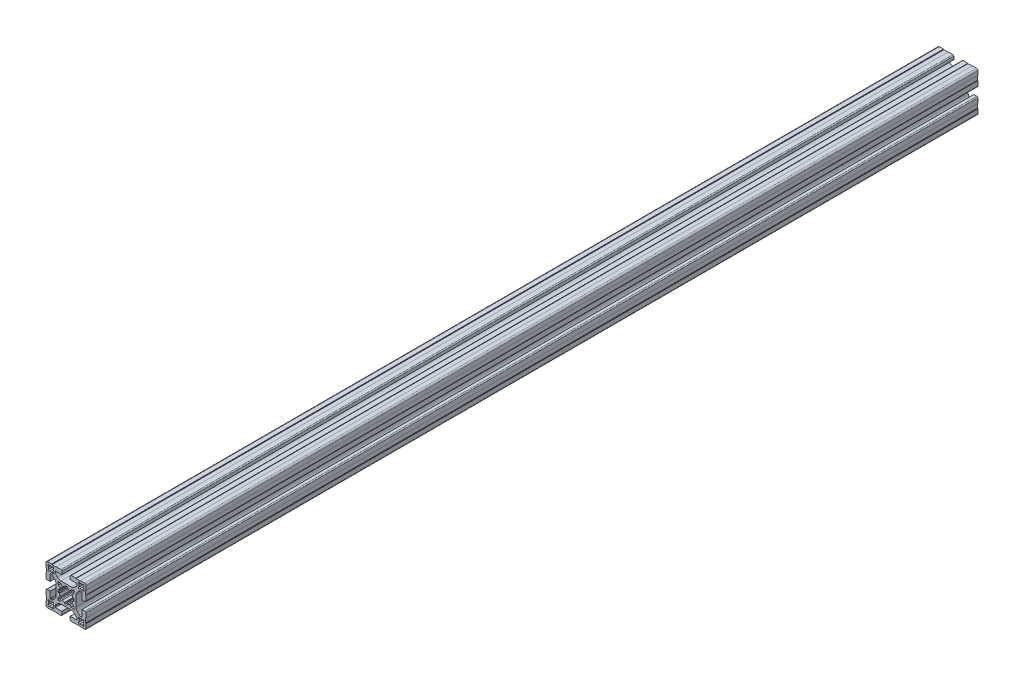
SolidWorks part; units mm, degrees
ref_plane "Plano frontal" through (0, 0, 0) normal (0, 0, 1) x (1, 0, 0)
ref_plane "Plano superior" through (0, 0, 0) normal (0, 1, 0) x (1, 0, 0)
ref_plane "Plano direito" through (0, 0, 0) normal (1, 0, 0) x (0, 0, -1)
sketch "Esboço1" plane through (0, 0, 0) normal (0, 0, 1) x (1, 0, 0)
  point P0 (0, 0)
  line B0 (-17.8572, 16.7966) -> (-17.4167, 16.356)
  arc B1 (-16.7966, 17.8572) -> (-17.8572, 16.7966) centre (-17.3269, 17.3269) ccw
  line B2 (-16.356, 17.4167) -> (-16.7966, 17.8572)
  arc B3 (-14.044, 17.4167) -> (-16.356, 17.4167) centre (-15.2, 15.2) ccw
  line B4 (-13.6034, 17.8572) -> (-14.044, 17.4167)
  arc B5 (-12.5428, 16.7966) -> (-13.6034, 17.8572) centre (-13.0731, 17.3269) ccw
  line B6 (-12.9833, 16.356) -> (-12.5428, 16.7966)
  arc B7 (-12.9833, 14.044) -> (-12.9833, 16.356) centre (-15.2, 15.2) ccw
  line B8 (-12.5428, 13.6034) -> (-12.9833, 14.044)
  arc B9 (-13.6034, 12.5428) -> (-12.5428, 13.6034) centre (-13.0731, 13.0731) ccw
  line B10 (-14.044, 12.9833) -> (-13.6034, 12.5428)
  arc B11 (-16.356, 12.9833) -> (-14.044, 12.9833) centre (-15.2, 15.2) ccw
  line B12 (-16.7966, 12.5428) -> (-16.356, 12.9833)
  arc B13 (-17.8572, 13.6034) -> (-16.7966, 12.5428) centre (-17.3269, 13.0731) ccw
  line B14 (-17.4167, 14.044) -> (-17.8572, 13.6034)
  arc B15 (-17.4167, 16.356) -> (-17.4167, 14.044) centre (-15.2, 15.2) ccw
  line B16 (17.4167, 14.044) -> (17.8572, 13.6034)
  arc B17 (16.7966, 12.5428) -> (17.8572, 13.6034) centre (17.3269, 13.0731) ccw
  line B18 (16.7966, 12.5428) -> (16.356, 12.9833)
  arc B19 (14.044, 12.9833) -> (16.356, 12.9833) centre (15.2, 15.2) ccw
  line B20 (14.044, 12.9833) -> (13.6034, 12.5428)
  arc B21 (12.5428, 13.6034) -> (13.6034, 12.5428) centre (13.0731, 13.0731) ccw
  line B22 (12.5428, 13.6034) -> (12.9833, 14.044)
  arc B23 (12.9833, 16.356) -> (12.9833, 14.044) centre (15.2, 15.2) ccw
  line B24 (12.9833, 16.356) -> (12.5428, 16.7966)
  arc B25 (13.6034, 17.8572) -> (12.5428, 16.7966) centre (13.0731, 17.3269) ccw
  line B26 (13.6034, 17.8572) -> (14.044, 17.4167)
  arc B27 (16.356, 17.4167) -> (14.044, 17.4167) centre (15.2, 15.2) ccw
  line B28 (16.356, 17.4167) -> (16.7966, 17.8572)
  arc B29 (17.8572, 16.7966) -> (16.7966, 17.8572) centre (17.3269, 17.3269) ccw
  line B30 (17.8572, 16.7966) -> (17.4167, 16.356)
  arc B31 (17.4167, 14.044) -> (17.4167, 16.356) centre (15.2, 15.2) ccw
  line B32 (-17.4167, -14.044) -> (-17.8572, -13.6034)
  arc B33 (-16.7966, -12.5428) -> (-17.8572, -13.6034) centre (-17.3269, -13.0731) ccw
  line B34 (-16.7966, -12.5428) -> (-16.356, -12.9833)
  arc B35 (-14.044, -12.9833) -> (-16.356, -12.9833) centre (-15.2, -15.2) ccw
  line B36 (-14.044, -12.9833) -> (-13.6034, -12.5428)
  arc B37 (-12.5428, -13.6034) -> (-13.6034, -12.5428) centre (-13.0731, -13.0731) ccw
  line B38 (-12.5428, -13.6034) -> (-12.9833, -14.044)
  arc B39 (-12.9833, -16.356) -> (-12.9833, -14.044) centre (-15.2, -15.2) ccw
  line B40 (-12.9833, -16.356) -> (-12.5428, -16.7966)
  arc B41 (-13.6034, -17.8572) -> (-12.5428, -16.7966) centre (-13.0731, -17.3269) ccw
  line B42 (-13.6034, -17.8572) -> (-14.044, -17.4167)
  arc B43 (-16.356, -17.4167) -> (-14.044, -17.4167) centre (-15.2, -15.2) ccw
  line B44 (-16.356, -17.4167) -> (-16.7966, -17.8572)
  arc B45 (-17.8572, -16.7966) -> (-16.7966, -17.8572) centre (-17.3269, -17.3269) ccw
  line B46 (-17.8572, -16.7966) -> (-17.4167, -16.356)
  arc B47 (-17.4167, -14.044) -> (-17.4167, -16.356) centre (-15.2, -15.2) ccw
  line B48 (17.8572, -16.7966) -> (17.4167, -16.356)
  arc B49 (16.7966, -17.8572) -> (17.8572, -16.7966) centre (17.3269, -17.3269) ccw
  line B50 (16.356, -17.4167) -> (16.7966, -17.8572)
  arc B51 (14.044, -17.4167) -> (16.356, -17.4167) centre (15.2, -15.2) ccw
  line B52 (13.6034, -17.8572) -> (14.044, -17.4167)
  arc B53 (12.5428, -16.7966) -> (13.6034, -17.8572) centre (13.0731, -17.3269) ccw
  line B54 (12.9833, -16.356) -> (12.5428, -16.7966)
  arc B55 (12.9833, -14.044) -> (12.9833, -16.356) centre (15.2, -15.2) ccw
  line B56 (12.5428, -13.6034) -> (12.9833, -14.044)
  arc B57 (13.6034, -12.5428) -> (12.5428, -13.6034) centre (13.0731, -13.0731) ccw
  line B58 (14.044, -12.9833) -> (13.6034, -12.5428)
  arc B59 (16.356, -12.9833) -> (14.044, -12.9833) centre (15.2, -15.2) ccw
  line B60 (16.7966, -12.5428) -> (16.356, -12.9833)
  arc B61 (17.8572, -13.6034) -> (16.7966, -12.5428) centre (17.3269, -13.0731) ccw
  line B62 (17.4167, -14.044) -> (17.8572, -13.6034)
  arc B63 (17.4167, -16.356) -> (17.4167, -14.044) centre (15.2, -15.2) ccw
  line B64 (4.15, -18.8) -> (4.15, -15.9)
  arc B65 (4.25, -15.8) -> (4.15, -15.9) centre (4.25, -15.9) ccw
  line B66 (4.25, -15.8) -> (10.5, -15.8)
  arc B67 (10.5, -15.8) -> (11, -15.3) centre (10.5, -15.3) ccw
  line B68 (11, -15.3) -> (11, -14.4497)
  arc B69 (11, -14.4497) -> (10.5607, -13.3891) centre (9.5, -14.4497) ccw
  line B70 (10.5607, -13.3891) -> (8.636, -11.4645)
  arc B71 (8.636, -11.4645) -> (5.1005, -10) centre (5.1005, -15) ccw
  line B72 (5.1005, -10) -> (0, -10)
  line B73 (0, -10) -> (-5.1005, -10)
  arc B74 (-5.1005, -10) -> (-8.636, -11.4645) centre (-5.1005, -15) ccw
  line B75 (-8.636, -11.4645) -> (-10.5607, -13.3891)
  arc B76 (-10.5607, -13.3891) -> (-11, -14.4497) centre (-9.5, -14.4497) ccw
  line B77 (-11, -14.4497) -> (-11, -15.3)
  arc B78 (-11, -15.3) -> (-10.5, -15.8) centre (-10.5, -15.3) ccw
  line B79 (-10.5, -15.8) -> (-4.25, -15.8)
  arc B80 (-4.15, -15.9) -> (-4.25, -15.8) centre (-4.25, -15.9) ccw
  line B81 (-4.15, -15.9) -> (-4.15, -18.8)
  arc B82 (-5.15, -19.8) -> (-4.15, -18.8) centre (-5.15, -18.8) ccw
  line B83 (-5.15, -19.8) -> (-9.8, -19.8)
  line B84 (-9.8, -19.8) -> (-10, -19.6)
  line B85 (-10, -19.6) -> (-14, -19.6)
  line B86 (-14, -19.6) -> (-14.4, -20)
  line B87 (-14.4, -20) -> (-18.5, -20)
  arc B88 (-20, -18.5) -> (-18.5, -20) centre (-18.5, -18.5) ccw
  line B89 (-20, -18.5) -> (-20, -14.4)
  line B90 (-20, -14.4) -> (-19.6, -14)
  line B91 (-19.6, -14) -> (-19.6, -10)
  line B92 (-19.6, -10) -> (-19.8, -9.8)
  line B93 (-19.8, -9.8) -> (-19.8, -5.15)
  arc B94 (-18.8, -4.15) -> (-19.8, -5.15) centre (-18.8, -5.15) ccw
  line B95 (-18.8, -4.15) -> (-15.9, -4.15)
  arc B96 (-15.8, -4.25) -> (-15.9, -4.15) centre (-15.9, -4.25) ccw
  line B97 (-15.8, -4.25) -> (-15.8, -10.5)
  arc B98 (-15.8, -10.5) -> (-15.3, -11) centre (-15.3, -10.5) ccw
  line B99 (-15.3, -11) -> (-14.4497, -11)
  arc B100 (-14.4497, -11) -> (-13.3891, -10.5607) centre (-14.4497, -9.5) ccw
  line B101 (-13.3891, -10.5607) -> (-11.4645, -8.636)
  arc B102 (-11.4645, -8.636) -> (-10, -5.1005) centre (-15, -5.1005) ccw
  line B103 (-10, -5.1005) -> (-10, 0)
  line B104 (-10, 0) -> (-10, 5.1005)
  arc B105 (-10, 5.1005) -> (-11.4645, 8.636) centre (-15, 5.1005) ccw
  line B106 (-11.4645, 8.636) -> (-13.3891, 10.5607)
  arc B107 (-13.3891, 10.5607) -> (-14.4497, 11) centre (-14.4497, 9.5) ccw
  line B108 (-14.4497, 11) -> (-15.3, 11)
  arc B109 (-15.3, 11) -> (-15.8, 10.5) centre (-15.3, 10.5) ccw
  line B110 (-15.8, 10.5) -> (-15.8, 4.25)
  arc B111 (-15.9, 4.15) -> (-15.8, 4.25) centre (-15.9, 4.25) ccw
  line B112 (-15.9, 4.15) -> (-18.8, 4.15)
  arc B113 (-19.8, 5.15) -> (-18.8, 4.15) centre (-18.8, 5.15) ccw
  line B114 (-19.8, 5.15) -> (-19.8, 9.8)
  line B115 (-19.8, 9.8) -> (-19.6, 10)
  line B116 (-19.6, 10) -> (-19.6, 14)
  line B117 (-19.6, 14) -> (-20, 14.4)
  line B118 (-20, 14.4) -> (-20, 18.5)
  arc B119 (-18.5, 20) -> (-20, 18.5) centre (-18.5, 18.5) ccw
  line B120 (-18.5, 20) -> (-14.4, 20)
  line B121 (-14.4, 20) -> (-14, 19.6)
  line B122 (-14, 19.6) -> (-10, 19.6)
  line B123 (-10, 19.6) -> (-9.8, 19.8)
  line B124 (-9.8, 19.8) -> (-5.15, 19.8)
  arc B125 (-4.15, 18.8) -> (-5.15, 19.8) centre (-5.15, 18.8) ccw
  line B126 (-4.15, 18.8) -> (-4.15, 15.9)
  arc B127 (-4.25, 15.8) -> (-4.15, 15.9) centre (-4.25, 15.9) ccw
  line B128 (-4.25, 15.8) -> (-10.5, 15.8)
  arc B129 (-10.5, 15.8) -> (-11, 15.3) centre (-10.5, 15.3) ccw
  line B130 (-11, 15.3) -> (-11, 14.4497)
  arc B131 (-11, 14.4497) -> (-10.5607, 13.3891) centre (-9.5, 14.4497) ccw
  line B132 (-10.5607, 13.3891) -> (-8.636, 11.4645)
  arc B133 (-8.636, 11.4645) -> (-5.1005, 10) centre (-5.1005, 15) ccw
  line B134 (-5.1005, 10) -> (0, 10)
  line B135 (0, 10) -> (5.1005, 10)
  arc B136 (5.1005, 10) -> (8.636, 11.4645) centre (5.1005, 15) ccw
  line B137 (8.636, 11.4645) -> (10.5607, 13.3891)
  arc B138 (10.5607, 13.3891) -> (11, 14.4497) centre (9.5, 14.4497) ccw
  line B139 (11, 14.4497) -> (11, 15.3)
  arc B140 (11, 15.3) -> (10.5, 15.8) centre (10.5, 15.3) ccw
  line B141 (10.5, 15.8) -> (4.25, 15.8)
  arc B142 (4.15, 15.9) -> (4.25, 15.8) centre (4.25, 15.9) ccw
  line B143 (4.15, 15.9) -> (4.15, 18.8)
  arc B144 (5.15, 19.8) -> (4.15, 18.8) centre (5.15, 18.8) ccw
  line B145 (5.15, 19.8) -> (9.8, 19.8)
  line B146 (9.8, 19.8) -> (10, 19.6)
  line B147 (10, 19.6) -> (14, 19.6)
  line B148 (14, 19.6) -> (14.4, 20)
  line B149 (14.4, 20) -> (18.5, 20)
  arc B150 (20, 18.5) -> (18.5, 20) centre (18.5, 18.5) ccw
  line B151 (20, 18.5) -> (20, 14.4)
  line B152 (20, 14.4) -> (19.6, 14)
  line B153 (19.6, 14) -> (19.6, 10)
  line B154 (19.6, 10) -> (19.8, 9.8)
  line B155 (19.8, 9.8) -> (19.8, 5.15)
  arc B156 (18.8, 4.15) -> (19.8, 5.15) centre (18.8, 5.15) ccw
  line B157 (18.8, 4.15) -> (15.9, 4.15)
  arc B158 (15.8, 4.25) -> (15.9, 4.15) centre (15.9, 4.25) ccw
  line B159 (15.8, 4.25) -> (15.8, 10.5)
  arc B160 (15.8, 10.5) -> (15.3, 11) centre (15.3, 10.5) ccw
  line B161 (15.3, 11) -> (14.4497, 11)
  arc B162 (14.4497, 11) -> (13.3891, 10.5607) centre (14.4497, 9.5) ccw
  line B163 (13.3891, 10.5607) -> (11.4645, 8.636)
  arc B164 (11.4645, 8.636) -> (10, 5.1005) centre (15, 5.1005) ccw
  line B165 (10, 5.1005) -> (10, 0)
  line B166 (10, 0) -> (10, -5.1005)
  arc B167 (10, -5.1005) -> (11.4645, -8.636) centre (15, -5.1005) ccw
  line B168 (11.4645, -8.636) -> (13.3891, -10.5607)
  arc B169 (13.3891, -10.5607) -> (14.4497, -11) centre (14.4497, -9.5) ccw
  line B170 (14.4497, -11) -> (15.3, -11)
  arc B171 (15.3, -11) -> (15.8, -10.5) centre (15.3, -10.5) ccw
  line B172 (15.8, -10.5) -> (15.8, -4.25)
  arc B173 (15.9, -4.15) -> (15.8, -4.25) centre (15.9, -4.25) ccw
  line B174 (15.9, -4.15) -> (18.8, -4.15)
  arc B175 (19.8, -5.15) -> (18.8, -4.15) centre (18.8, -5.15) ccw
  line B176 (19.8, -5.15) -> (19.8, -9.8)
  line B177 (19.8, -9.8) -> (19.6, -10)
  line B178 (19.6, -10) -> (19.6, -14)
  line B179 (19.6, -14) -> (20, -14.4)
  line B180 (20, -14.4) -> (20, -18.5)
  arc B181 (18.5, -20) -> (20, -18.5) centre (18.5, -18.5) ccw
  line B182 (18.5, -20) -> (14.4, -20)
  line B183 (14.4, -20) -> (14, -19.6)
  line B184 (14, -19.6) -> (10, -19.6)
  line B185 (10, -19.6) -> (9.8, -19.8)
  line B186 (9.8, -19.8) -> (5.15, -19.8)
  arc B187 (4.15, -18.8) -> (5.15, -19.8) centre (5.15, -18.8) ccw
  line B188 (-5.3139, -7.6355) -> (-7.6488, -8.2611)
  arc B189 (-8.2611, -7.6488) -> (-7.6488, -8.2611) centre (-7.7782, -7.7782) ccw
  line B190 (-8.2611, -7.6488) -> (-7.6355, -5.3139)
  arc B191 (-7.4569, -5.0466) -> (-7.6355, -5.3139) centre (-7.1525, -5.4433) ccw
  line B192 (-7.4569, -5.0466) -> (-5.744, -3.7322)
  arc B193 (-6.7007, -1.4225) -> (-5.744, -3.7322) centre (0, 0) ccw
  line B194 (-6.7007, -1.4225) -> (-7.5204, -1.3146)
  arc B195 (-7.9522, -0.8735) -> (-7.5204, -1.3146) centre (-7.4552, -0.8189) ccw
  arc B196 (-7.9522, 0.8735) -> (-7.9522, -0.8735) centre (0, 0) ccw
  arc B197 (-7.5204, 1.3146) -> (-7.9522, 0.8735) centre (-7.4552, 0.8189) ccw
  line B198 (-7.5204, 1.3146) -> (-6.7007, 1.4225)
  arc B199 (-5.744, 3.7322) -> (-6.7007, 1.4225) centre (0, 0) ccw
  line B200 (-5.744, 3.7322) -> (-7.4569, 5.0466)
  arc B201 (-7.6355, 5.3139) -> (-7.4569, 5.0466) centre (-7.1525, 5.4433) ccw
  line B202 (-7.6355, 5.3139) -> (-8.2611, 7.6488)
  arc B203 (-7.6488, 8.2611) -> (-8.2611, 7.6488) centre (-7.7782, 7.7782) ccw
  line B204 (-7.6488, 8.2611) -> (-5.3139, 7.6355)
  arc B205 (-5.0466, 7.4569) -> (-5.3139, 7.6355) centre (-5.4433, 7.1525) ccw
  line B206 (-5.0466, 7.4569) -> (-3.7322, 5.744)
  arc B207 (-1.4225, 6.7007) -> (-3.7322, 5.744) centre (0, 0) ccw
  line B208 (-1.4225, 6.7007) -> (-1.3146, 7.5204)
  arc B209 (-0.8735, 7.9522) -> (-1.3146, 7.5204) centre (-0.8189, 7.4552) ccw
  arc B210 (0.8735, 7.9522) -> (-0.8735, 7.9522) centre (0, 0) ccw
  arc B211 (1.3146, 7.5204) -> (0.8735, 7.9522) centre (0.8189, 7.4552) ccw
  line B212 (1.3146, 7.5204) -> (1.4225, 6.7007)
  arc B213 (3.7322, 5.744) -> (1.4225, 6.7007) centre (0, 0) ccw
  line B214 (3.7322, 5.744) -> (5.0466, 7.4569)
  arc B215 (5.3139, 7.6355) -> (5.0466, 7.4569) centre (5.4433, 7.1525) ccw
  line B216 (5.3139, 7.6355) -> (7.6488, 8.2611)
  arc B217 (8.2611, 7.6488) -> (7.6488, 8.2611) centre (7.7782, 7.7782) ccw
  line B218 (8.2611, 7.6488) -> (7.6355, 5.3139)
  arc B219 (7.4569, 5.0466) -> (7.6355, 5.3139) centre (7.1525, 5.4433) ccw
  line B220 (7.4569, 5.0466) -> (5.744, 3.7322)
  arc B221 (6.7007, 1.4225) -> (5.744, 3.7322) centre (0, 0) ccw
  line B222 (6.7007, 1.4225) -> (7.5204, 1.3146)
  arc B223 (7.9522, 0.8735) -> (7.5204, 1.3146) centre (7.4552, 0.8189) ccw
  arc B224 (7.9522, -0.8735) -> (7.9522, 0.8735) centre (0, 0) ccw
  arc B225 (7.5204, -1.3146) -> (7.9522, -0.8735) centre (7.4552, -0.8189) ccw
  line B226 (7.5204, -1.3146) -> (6.7007, -1.4225)
  arc B227 (5.744, -3.7322) -> (6.7007, -1.4225) centre (0, 0) ccw
  line B228 (5.744, -3.7322) -> (7.4569, -5.0466)
  arc B229 (7.6355, -5.3139) -> (7.4569, -5.0466) centre (7.1525, -5.4433) ccw
  line B230 (7.6355, -5.3139) -> (8.2611, -7.6488)
  arc B231 (7.6488, -8.2611) -> (8.2611, -7.6488) centre (7.7782, -7.7782) ccw
  line B232 (7.6488, -8.2611) -> (5.3139, -7.6355)
  arc B233 (5.0466, -7.4569) -> (5.3139, -7.6355) centre (5.4433, -7.1525) ccw
  line B234 (5.0466, -7.4569) -> (3.7322, -5.744)
  arc B235 (1.4225, -6.7007) -> (3.7322, -5.744) centre (0, 0) ccw
  line B236 (1.4225, -6.7007) -> (1.3146, -7.5204)
  arc B237 (0.8735, -7.9522) -> (1.3146, -7.5204) centre (0.8189, -7.4552) ccw
  arc B238 (-0.8735, -7.9522) -> (0.8735, -7.9522) centre (0, 0) ccw
  arc B239 (-1.3146, -7.5204) -> (-0.8735, -7.9522) centre (-0.8189, -7.4552) ccw
  line B240 (-1.3146, -7.5204) -> (-1.4225, -6.7007)
  arc B241 (-3.7322, -5.744) -> (-1.4225, -6.7007) centre (0, 0) ccw
  line B242 (-3.7322, -5.744) -> (-5.0466, -7.4569)
  arc B243 (-5.3139, -7.6355) -> (-5.0466, -7.4569) centre (-5.4433, -7.1525) ccw
sketch_block_instance "P40103-1"
sketch_block "P40103"
other "Item de detalhe3"
other "Item de detalhe4"
extrude "Ressalto-extrusão1" add sketch "Esboço1" along normal mid plane 890
